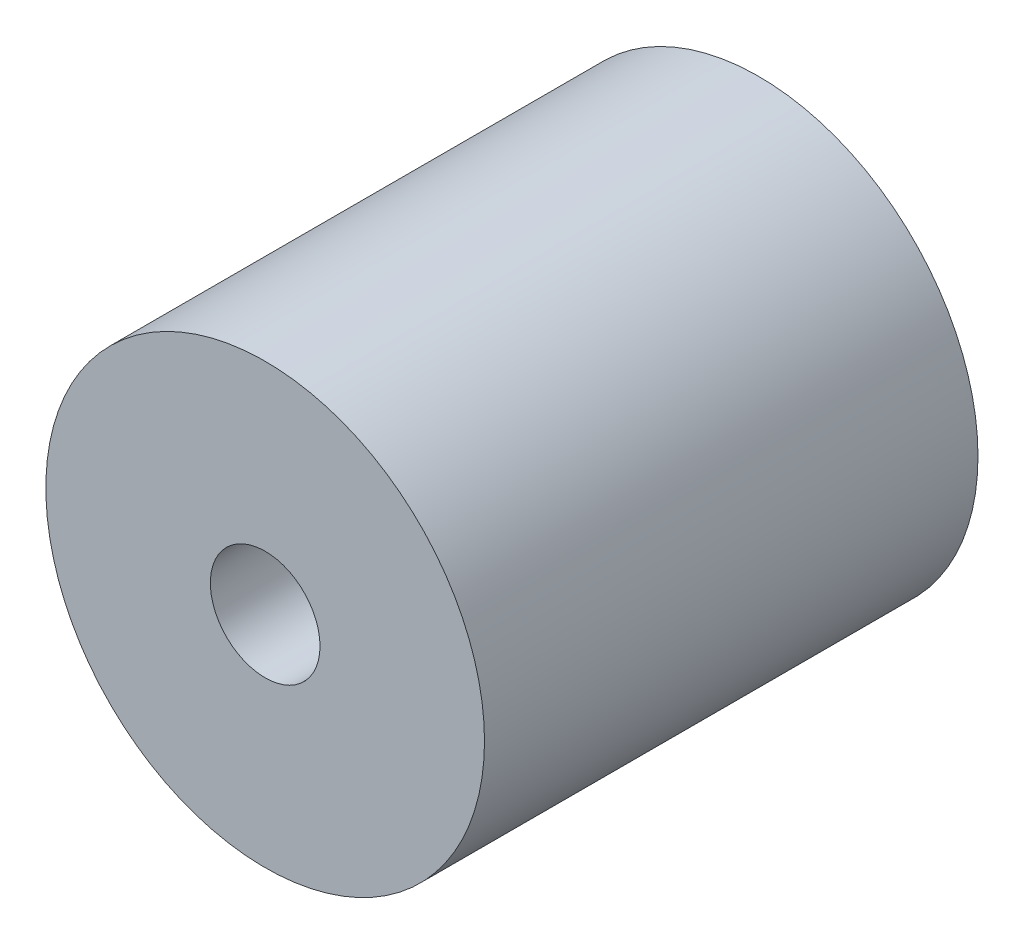
SolidWorks part; units mm, degrees
ref_plane "Front Plane" through (0, 0, 0) normal (0, 0, 1) x (1, 0, 0)
ref_plane "Top Plane" through (0, 0, 0) normal (0, 1, 0) x (1, 0, 0)
ref_plane "Right Plane" through (0, 0, 0) normal (1, 0, 0) x (0, 0, -1)
sketch "Sketch1" plane through (0, 0, 0) normal (0, 0, 1) x (1, 0, 0)
  circle A0 centre (0, 0) radius 10
  circle A1 centre (0, 0) radius 40
  dimension "D1" = 20
  dimension "D2" = 80
extrude "Boss-Extrude1" add sketch "Sketch1" along normal blind 90
